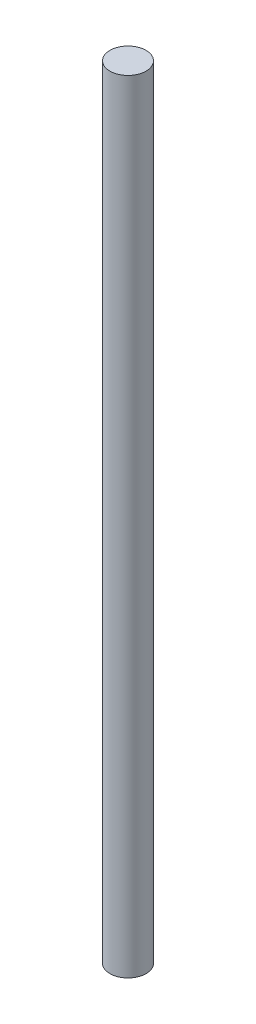
SolidWorks part; units mm, degrees
ref_plane "Front Plane" through (0, 0, 0) normal (0, 0, 1) x (1, 0, 0)
ref_plane "Top Plane" through (0, 0, 0) normal (0, 1, 0) x (1, 0, 0)
ref_plane "Right Plane" through (0, 0, 0) normal (1, 0, 0) x (0, 0, -1)
sketch "Sketch1" plane through (0, 0, 0) normal (0, 1, 0) x (1, 0, 0)
  circle A0 centre (0, 0) radius 3
  dimension "D1" = 6
extrude "Boss-Extrude1" add sketch "Sketch1" along normal blind 130
